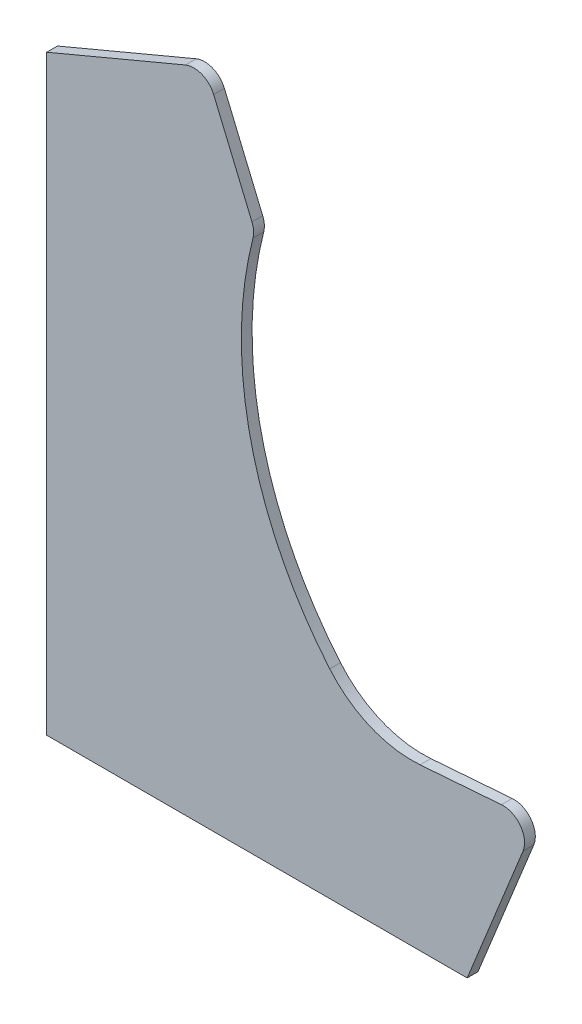
SolidWorks part; units mm, degrees
ref_plane "Plan de face" through (0, 0, 0) normal (0, 0, 1) x (1, 0, 0)
ref_plane "Plan de dessus" through (0, 0, 0) normal (0, 1, 0) x (1, 0, 0)
ref_plane "Plan de droite" through (0, 0, 0) normal (1, 0, 0) x (0, 0, -1)
sketch "Esquisse1" plane through (0, 0, 0) normal (0, 0, 1) x (1, 0, 0)
  line L0 (0, 0) -> (0, 550)
  line L1 (0, 0) -> (391, 0)
  line L2 (0, 550) -> (129.0626, 604.25)
  line L3 (155.25, 593.5626) -> (190.859, 508.8475)
  line L4 (391, 0) -> (442.8892, 128.0248)
  line L5 (422.8495, 155.4807) -> (347.1605, 149.7719)
  arc A0 (191.8026, 496.16) -> (263.1894, 185.0263) centre (530, 410) ccw
  arc A1 (155.25, 593.5626) -> (129.0626, 604.25) centre (136.8126, 585.8126) ccw
  arc A2 (422.8495, 155.4807) -> (442.8892, 128.0248) centre (424.3537, 135.5374) cw
  arc A3 (191.8026, 496.16) -> (190.859, 508.8475) centre (172.4216, 501.0975) ccw
  arc A4 (347.1605, 149.7719) -> (263.1894, 185.0263) centre (339.6394, 249.4887) cw
  point P12 (147.5, 612)
  point P15 (455, 157.9056)
  point P18 (193.9979, 501.38)
  point P20 (193.4994, 502.5658)
  point P21 (301.3674, 146.318)
  dimension "D12" = 356.2478
  dimension "D13" = 20
  dimension "D14" = 20
  dimension "D15" = 20
  dimension "D7" = 100
  dimension "D1" = 391
  dimension "D2" = 550
  dimension "D3" = 62
  dimension "D4" = 147.5
  dimension "D5" = 110.62
  dimension "D6" = 455
  dimension "D9" = 107.8679
  dimension "D10" = 530
  dimension "D11" = 410
extrude "Boss.-Extru.1" add sketch "Esquisse1" along normal blind 10
